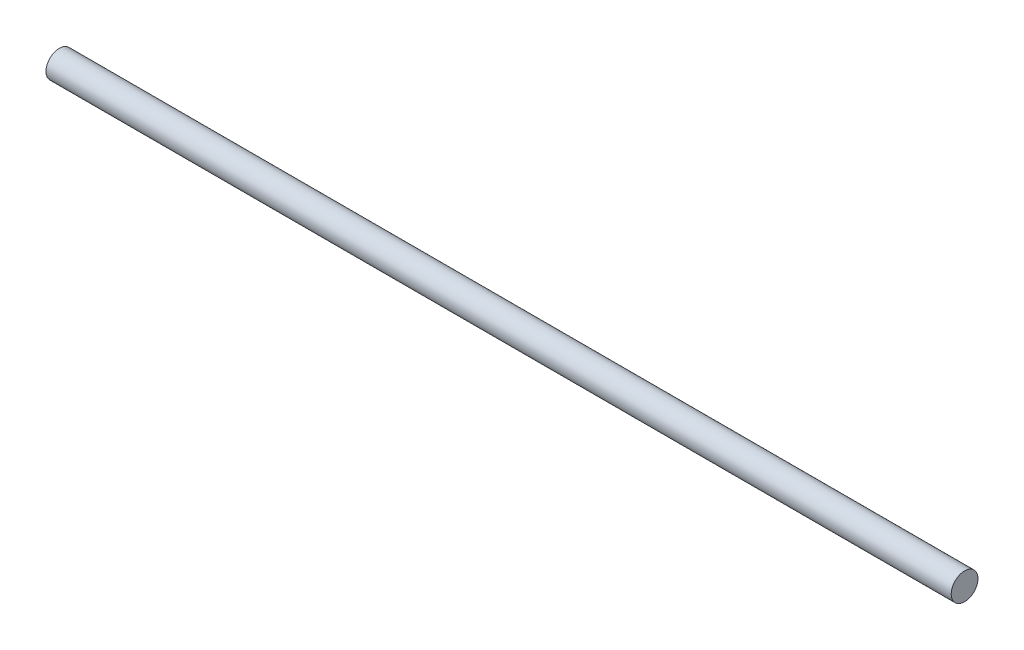
SolidWorks part; units mm, degrees
ref_plane "Front Plane" through (0, 0, 0) normal (0, 0, 1) x (1, 0, 0)
ref_plane "Top Plane" through (0, 0, 0) normal (0, 1, 0) x (1, 0, 0)
ref_plane "Right Plane" through (0, 0, 0) normal (1, 0, 0) x (0, 0, -1)
sketch "Sketch1" plane through (0, 0, 0) normal (1, 0, 0) x (0, 0, -1)
  circle A0 centre (0, 0) radius 14.2875
  dimension "D1" = 28.575
extrude "Boss-Extrude1" add sketch "Sketch1" along normal mid plane 965.2
